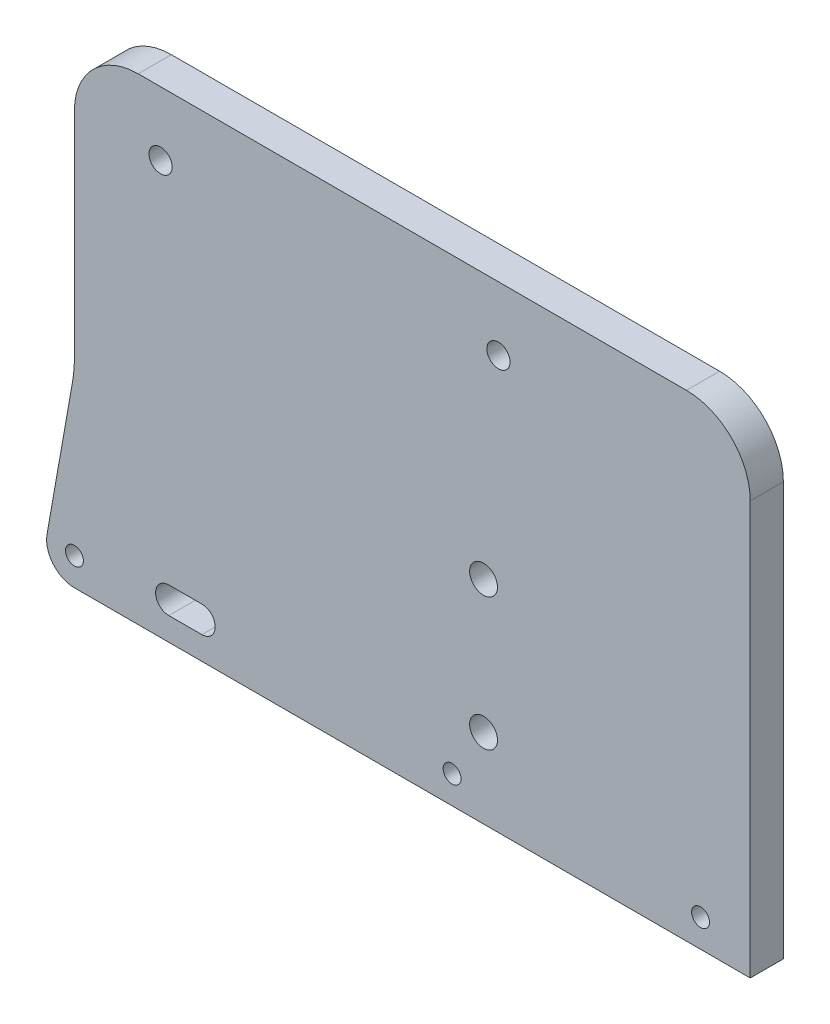
SolidWorks part; units mm, degrees
material "6061-T6 Black anodised"
ref_plane "Front Plane" through (0, 0, 0) normal (0, 0, 1) x (1, 0, 0)
ref_plane "Top Plane" through (0, 0, 0) normal (0, 1, 0) x (1, 0, 0)
ref_plane "Right Plane" through (0, 0, 0) normal (1, 0, 0) x (0, 0, -1)
sketch "Sketch1" plane through (0, 0, 0) normal (0, 0, 1) x (1, 0, 0)
  line L0 (-62.0538, 14.6636) -> (-65.8862, -7.0707)
  line L1 (0, 24.8959) -> (0, 0) construction
  line L2 (0, 0) -> (0, -5) construction
  line L3 (-61.75, -12) -> (40.25, -12)
  line L4 (-47.5, -6.5) -> (-42.5, -6.5) construction
  line L5 (-52.12, 60) -> (30.62, 60)
  line L6 (40.25, -12) -> (40.25, 50.37)
  line L7 (-47.5, -4.5) -> (-42.5, -4.5)
  line L8 (-61.75, 18.1366) -> (-61.75, 50.37)
  line L9 (-47.5, -8.5) -> (-42.5, -8.5)
  circle A0 centre (0, 0) radius 2.1
  arc A1 (-62.0538, 14.6636) -> (-61.75, 18.1366) centre (-81.75, 18.1366) ccw
  circle A2 centre (-48.75, 50.37) radius 1.75
  arc A3 (-65.8862, -7.0707) -> (-61.75, -12) centre (-61.75, -7.8) ccw
  circle A4 centre (32.75, -7.8) radius 1.35
  arc A5 (-52.12, 60) -> (-61.75, 50.37) centre (-52.12, 50.37) ccw
  arc A6 (40.25, 50.37) -> (30.62, 60) centre (30.62, 50.37) ccw
  arc A7 (-47.5, -4.5) -> (-47.5, -8.5) centre (-47.5, -6.5) ccw
  circle A8 centre (2.25, 50.37) radius 1.75
  arc A9 (-42.5, -8.5) -> (-42.5, -4.5) centre (-42.5, -6.5) ccw
  circle A10 centre (-61.75, -7.8) radius 1.35
  circle A11 centre (-4.75, -7.8) radius 1.35
  circle A12 centre (0, 20) radius 2.1
  point P28 (-45, -6.5)
  dimension "D1" = 3.5
  dimension "D2" = 48.75
  dimension "D3" = 7.8
  dimension "D4" = 51
  dimension "D5" = 4.75
  dimension "D6" = 57
  dimension "D7" = 37.5
  dimension "D13" = 20
  dimension "D14" = 2.7
  dimension "D15" = 4.2
  dimension "D19" = 2
  dimension "D8" = 20
  dimension "D9" = 50.37
  dimension "D10" = 102
  dimension "D11" = 61.75
  dimension "D12" = 12
  dimension "D16" = 10
  dimension "D17" = 60
  dimension "D18" = 5
  dimension "D20" = 5.5
  dimension "D21" = 45
extrude "Boss-Extrude1" add sketch "Sketch1" along normal blind 5
